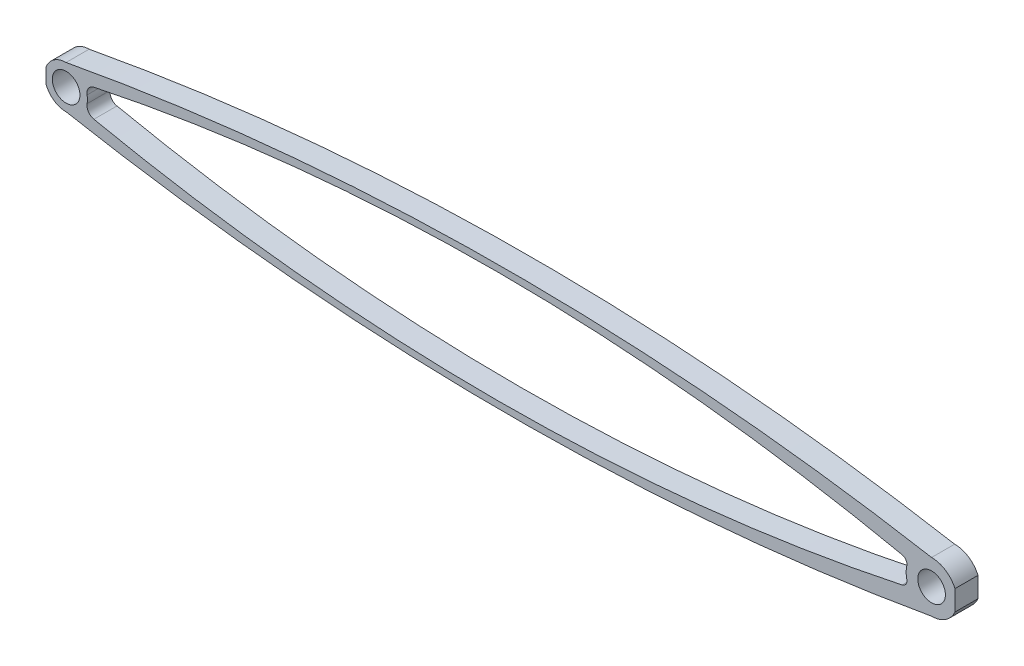
SolidWorks part; units mm, degrees
material "ABS"
ref_plane "Płaszczyzna przednia" through (0, 0, 0) normal (0, 0, 1) x (1, 0, 0)
ref_plane "Płaszczyzna górna" through (0, 0, 0) normal (0, 1, 0) x (1, 0, 0)
ref_plane "Płaszczyzna prawa" through (0, 0, 0) normal (1, 0, 0) x (0, 0, -1)
sketch "Szkic1" plane through (0, 0, 0) normal (0, 0, 1) x (1, 0, 0)
  line L0 (-3, 0) -> (187.7624, 0) construction
  line L1 (92.3812, 0) -> (92.3812, 21.7565) construction
  circle A0 centre (0, 0) radius 3
  circle A1 centre (187.7624, 0) radius 3
  circle A2 centre (187.7624, 0) radius 5.5226
  circle A3 centre (0, 0) radius 4.6352
  arc A4 (182.852, 2.5274) -> (3.8693, 2.5521) centre (93.3035, -412.1961) ccw
  arc A5 (187.7624, -5.5226) -> (0, -4.6352) centre (96.3223, 511.4169) cw
  arc A6 (187.7624, 5.5226) -> (0, 4.6352) centre (96.3223, -511.4169) ccw
  arc A7 (182.852, -2.5274) -> (3.8693, -2.5521) centre (93.3035, 412.1961) cw
  arc A8 (181.3535, -2.8481) -> (182.3804, -1.2383) centre (181.0756, -1.5384) ccw
  arc A9 (4.5614, 0.8238) -> (6.0352, 3.0132) centre (6.4246, 1.1603) cw
  arc A10 (4.5614, -0.8238) -> (6.0352, -3.0132) centre (6.4246, -1.1603) ccw
  arc A11 (181.3535, 2.8481) -> (182.3804, 1.2383) centre (181.0756, 1.5384) cw
  dimension "D1" = 187.7624
  dimension "D2" = 6
  dimension "D3" = 5.5226
  dimension "D4" = 4.6352
extrude "Dodanie-wyciągnięcie1" add sketch "Szkic1" along normal blind 5 contours A2 A6 A3 A4 | A2 A7 A3 A5 | A3 A0 | A10 A3 A7 | A3 A9 A4 | A8 A7 A2 | A2 A1 | A4 A11 A2
sketch "Szkic2" plane through (0, 0, 0) normal (0, 0, 1) x (1, 0, 0)
  line L0 (196.2931, 0) -> (-6.6873, 0) construction
  line L1 (192.8293, 4.1341) -> (192.8293, -3.3715)
  line L2 (-4.3568, -2.5646) -> (-4.3568, 2.4871)
  line L4 (-4.3568, 2.4871) -> (-5.0086, 2.4871)
  line L5 (-4.3568, 2.4871) -> (-4.3568, -2.5646)
  line L6 (-4.3568, -2.5646) -> (-5.0086, -2.5646)
  line L7 (-5.0086, 2.4871) -> (-5.0086, -2.5646)
  line L8 (192.8293, -3.3715) -> (194.4479, -3.3715)
  line L9 (192.8293, -3.3715) -> (192.8293, 4.1341)
  line L10 (192.8293, 4.1341) -> (194.4479, 4.1341)
  line L11 (194.4479, -3.3715) -> (194.4479, 4.1341)
extrude "Wytnij-wyciągnięcie3" cut sketch "Szkic2" along normal through all contours L0 L11 L10 L1 | L11 L0 L9 L8 | L0 L5 L4 L7 | L2 L0 L7 L6
